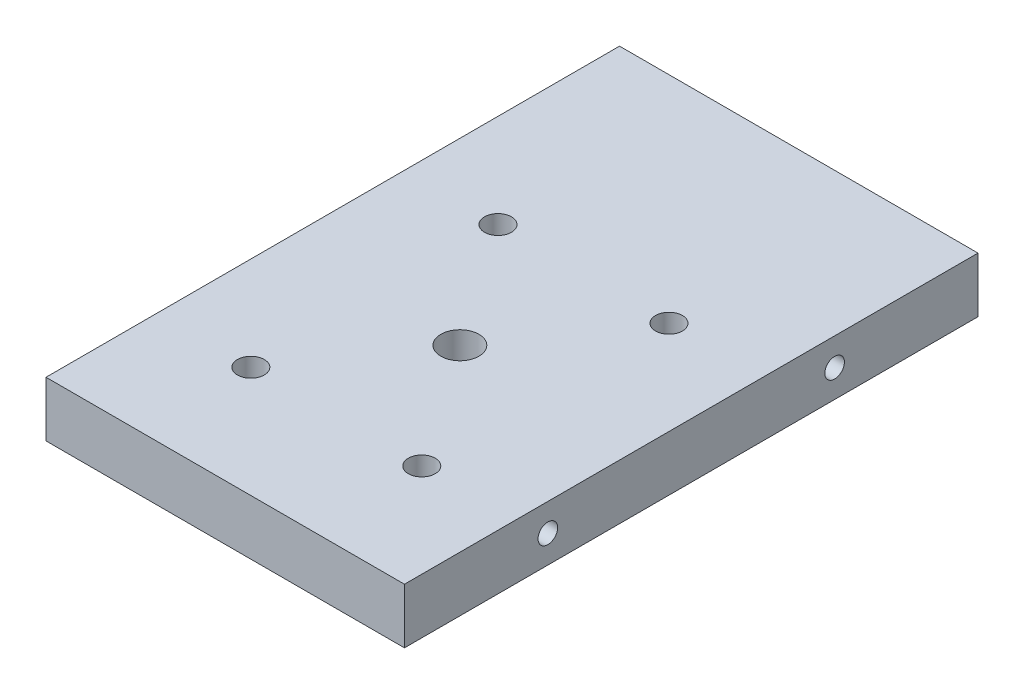
SolidWorks part; units mm, degrees
ref_plane "Front Plane" through (0, 0, 0) normal (0, 0, 1) x (1, 0, 0)
ref_plane "Top Plane" through (0, 0, 0) normal (0, 1, 0) x (1, 0, 0)
ref_plane "Right Plane" through (0, 0, 0) normal (1, 0, 0) x (0, 0, -1)
sketch "Sketch1" plane through (0, 0, 0) normal (0, 1, 0) x (1, 0, 0)
  line L1 (0, 0) -> (32.5, 0)
  line L2 (0, 0) -> (0, 52)
  line L3 (0, 52) -> (32.5, 52)
  line L4 (32.5, 0) -> (32.5, 52)
extrude "Boss-Extrude1" add sketch "Sketch1" along normal blind 5
sketch "Sketch2" plane through (0, 5, 0) normal (0, 1, 0) x (1, 0, 0)
  line L0 (0, 0) -> (0, 3)
  line L1 (0, 52) -> (0, 0) construction
  line L2 (0, 3) -> (32.5, 3)
  line L3 (32.5, 0) -> (32.5, 52) construction
  line L4 (0, 1.5) -> (32.5, 1.5)
  line L5 (16.25, 3) -> (0, 0)
  line L6 (16.25, 3) -> (32.5, 0)
  line L7 (0, 52) -> (0, 45)
  line L8 (0, 45) -> (32.5, 45)
  line L9 (0, 48.5) -> (32.5, 48.5)
  line L10 (0, 52) -> (16.25, 45)
  line L11 (16.25, 45) -> (32.5, 52)
sketch "Sketch4" plane through (0, 0, 0) normal (-1, 0, 0) x (0, 0, 1)
  line L0 (-52, 5) -> (-26, 0)
  line L1 (-52, 0) -> (0, 0) construction
  line L2 (-26, 0) -> (0, 5)
  line L3 (0, 5) -> (0, 0)
  line L4 (0, 0) -> (-26, 5)
  line L5 (-52, 5) -> (0, 5) construction
  line L6 (-26, 5) -> (-52, 0)
hole_wizard "#2-56 Tapped Hole1" positions "Sketch5" profile "Sketch6" tap size "#2-56" standard "ANSI Inch"
sketch "Sketch5" plane through (0, 0, 0) normal (-1, 0, 0) x (0, 0, 1)
  line L0 (-52, 5) -> (-26, 0) construction
  line L1 (-26, 0) -> (0, 5) construction
  point P0 (-39, 2.5)
  point P4 (-13, 2.5)
sketch "Sketch6" plane through (0, 2.5, -39) normal (0, 1, 0) x (0, 0, 1)
  line L0 (0, 0) -> (0, 8)
  line L1 (0, 8) -> (0.889, 7.4658)
  line L2 (0.889, 7.4658) -> (0.889, 0)
  line L5 (0.889, 0) -> (0, 0)
  line L10 (0, 8) -> (-0.889, 7.4658) construction
  line L11 (0, -6.35) -> (0, 107.95) construction
  dimension "Tap Drill Dia." = 1.778
  dimension "Tap Drill Depth" = 8
  dimension "Drill Angle" = 118
cosmetic thread "Hole Thread1" parameters "D1"=4.37, "D2"=2.1844
cosmetic thread "Hole Thread2" parameters "D1"=4.37, "D2"=2.1844
sketch "Sketch7" plane through (32.5, 0, 0) normal (1, 0, 0) x (0, 0, -1)
  line L0 (0, 5) -> (26, 0)
  line L1 (0, 0) -> (52, 0) construction
  line L2 (26, 0) -> (52, 5)
  line L3 (52, 5) -> (52, 0)
  line L4 (52, 0) -> (26, 5)
  line L5 (0, 5) -> (52, 5) construction
  line L6 (26, 5) -> (0, 0)
hole_wizard "#2-56 Tapped Hole2" positions "Sketch8" profile "Sketch9" tap size "#2-56" standard "ANSI Inch"
sketch "Sketch8" plane through (32.5, 0, 0) normal (1, 0, 0) x (0, 0, -1)
  line L0 (0, 5) -> (26, 0) construction
  line L1 (26, 0) -> (52, 5) construction
  point P0 (13, 2.5)
  point P4 (39, 2.5)
sketch "Sketch9" plane through (32.5, 2.5, -13) normal (0, 1, 0) x (0, 0, -1)
  line L0 (0, 0) -> (0, 8)
  line L1 (0, 8) -> (0.889, 7.4658)
  line L2 (0.889, 7.4658) -> (0.889, 0)
  line L5 (0.889, 0) -> (0, 0)
  line L10 (0, 8) -> (-0.889, 7.4658) construction
  line L11 (0, -6.35) -> (0, 107.95) construction
  dimension "Tap Drill Dia." = 1.778
  dimension "Tap Drill Depth" = 8
  dimension "Drill Angle" = 118
cosmetic thread "Hole Thread3" parameters "D1"=4.37, "D2"=2.1844
cosmetic thread "Hole Thread4" parameters "D1"=4.37, "D2"=2.1844
sketch "Sketch12" plane through (0, 5, 0) normal (0, 1, 0) x (1, 0, 0)
  line L0 (0, 0) -> (0, 21.275)
  line L1 (0, 52) -> (0, 0) construction
  line L2 (0, 21.275) -> (32.5, 21.275)
  line L3 (32.5, 0) -> (32.5, 52) construction
hole_wizard "#8-32 Tapped Hole1" positions "Sketch13" profile "Sketch14" tap size "#8-32" standard "ANSI Inch"
sketch "Sketch13" plane through (0, 5, 0) normal (0, 1, 0) x (1, 0, 0)
  line L0 (0, 21.275) -> (32.5, 21.275) construction
  point P0 (16.25, 21.275)
sketch "Sketch14" plane through (16.25, 5, -21.275) normal (1, 0, 0) x (0, 0, 1)
  line L0 (0, 0) -> (0, 10.71)
  line L1 (0, 10.71) -> (1.7272, 9.6722)
  line L2 (1.7272, 9.6722) -> (1.7272, 0)
  line L5 (1.7272, 0) -> (0, 0)
  line L10 (0, 10.71) -> (-1.7272, 9.6722) construction
  line L11 (0, -6.35) -> (0, 107.95) construction
  dimension "Tap Drill Dia." = 3.4544
  dimension "Tap Drill Depth" = 10.71
  dimension "Drill Angle" = 118
cosmetic thread "Hole Thread5" parameters "D1"=8.33, "D2"=4.1656
sketch "Sketch15" plane through (0, 5, 0) normal (0, 1, 0) x (1, 0, 0)
  line L0 (16.25, 21.275) -> (25.5, 21.275)
  line L1 (0, 21.275) -> (32.5, 21.275) construction
  line L2 (25.5, 21.275) -> (25.5, 33.98)
  line L3 (25.5, 33.98) -> (7, 33.98)
  line L4 (7, 33.98) -> (7, 8.57)
  line L5 (7, 8.57) -> (25.5, 8.57)
  line L6 (25.5, 8.57) -> (25.5, 21.275)
  line L7 (7, 33.98) -> (7, 32.48)
  line L8 (7, 32.48) -> (25.5, 32.48)
  line L9 (7, 33.98) -> (8.5, 33.98)
  line L10 (8.5, 33.98) -> (8.5, 8.57)
  line L11 (25.5, 33.98) -> (24, 33.98)
  line L12 (24, 33.98) -> (24, 8.57)
  line L13 (25.5, 8.57) -> (25.5, 10.07)
  line L14 (25.5, 10.07) -> (7, 10.07)
sketch "Sketch16" plane through (0, 5, 0) normal (0, 1, 0) x (1, 0, 0)
  line L1 (7, 32.48) -> (25.5, 32.48) construction
  line L2 (8.5, 33.98) -> (8.5, 8.57) construction
  line L4 (24, 33.98) -> (24, 8.57) construction
  line L6 (25.5, 10.07) -> (7, 10.07) construction
  circle A0 centre (8.5, 32.48) radius 1.22
  circle A1 centre (24, 32.48) radius 1.22
  circle A2 centre (8.5, 10.07) radius 1.22
  circle A3 centre (24, 10.07) radius 1.22
extrude "Cut-Extrude4" cut sketch "Sketch16" against normal blind 5
